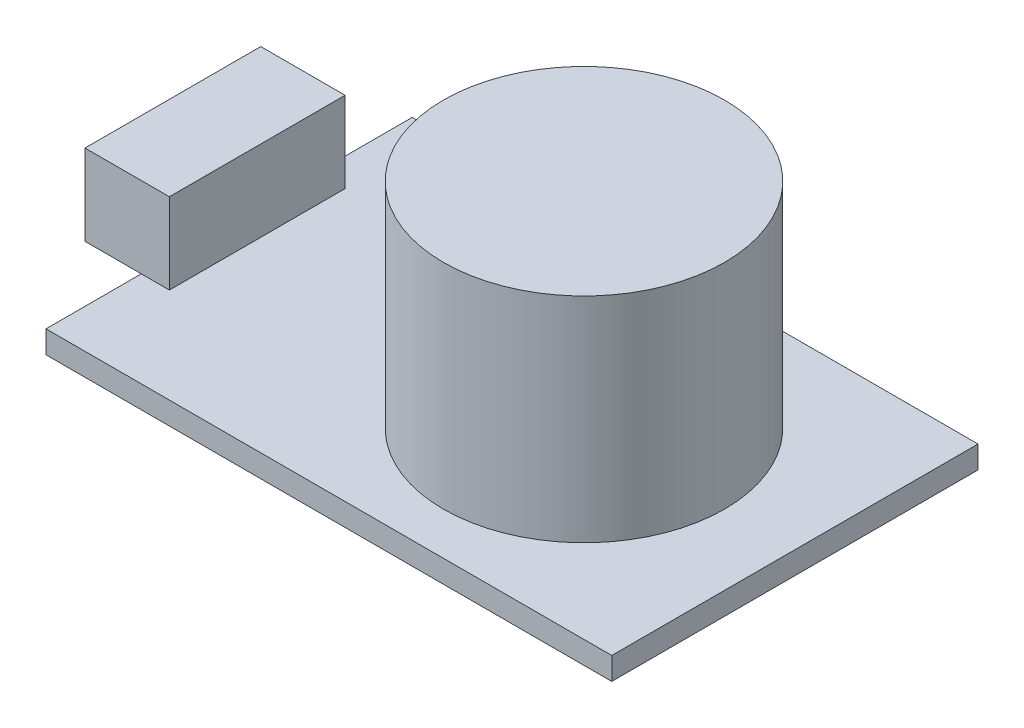
SolidWorks part; units mm, degrees
other "标注1"
sketch "草图5" plane through (40.24, 16.8, -26.05) normal (0.3542, 0.564, -0.746) x (-0.9014, 0.4183, -0.1117)
ref_plane "前视基准面" through (0, 0, 0) normal (0, 0, 1) x (1, 0, 0)
ref_plane "上视基准面" through (0, 0, 0) normal (0, 1, 0) x (1, 0, 0)
ref_plane "右视基准面" through (0, 0, 0) normal (1, 0, 0) x (0, 0, -1)
sketch "草图1" plane through (0, 0, 0) normal (0, 1, 0) x (1, 0, 0)
  line L0 (0, 0) -> (40.24, 0)
  line L1 (40.24, 0) -> (40.24, 26.05)
  line L2 (40.24, 26.05) -> (0, 26.05)
  line L3 (0, 26.05) -> (0, 0)
extrude "凸台-拉伸1" add sketch "草图1" along normal blind 1.6
sketch "草图2" plane through (0, 1.6, 0) normal (0, 1, 0) x (1, 0, 0)
  line L0 (0, 13.025) -> (40.24, 13.025)
  line L1 (0, 26.05) -> (0, 0) construction
  line L2 (40.24, 0) -> (40.24, 26.05) construction
  line L3 (40.24, 13.025) -> (25.24, 13.025)
  circle A0 centre (25.24, 13.025) radius 10
extrude "凸台-拉伸2" add sketch "草图2" along normal blind 15.2 contours L0 A0 | L0 A0
sketch "草图3" plane through (0, 0, 0) normal (-1, 0, 0) x (0, 0, 1)
  line L0 (-26.05, 1.6) -> (0, 1.6)
  line L1 (-13.025, 1.6) -> (-6.775, 1.6)
  line L2 (-13.025, 1.6) -> (-19.275, 1.6)
  line L3 (-19.275, 1.6) -> (-19.275, 7.35)
  line L4 (-19.275, 7.35) -> (-6.775, 7.35)
  line L5 (-6.775, 7.35) -> (-6.775, 1.6)
  line M8 (0, 1.6) -> (-26.05, 1.6)
extrude "凸台-拉伸3" add sketch "草图3" along normal blind 4 and the other way blind 2 contours L5 L4 L3 L0 M8
sketch "草图4" plane through (0, 0, 0) normal (0, -1, 0) x (1, 0, 0)
  point P0 (25.24, -13.025)
